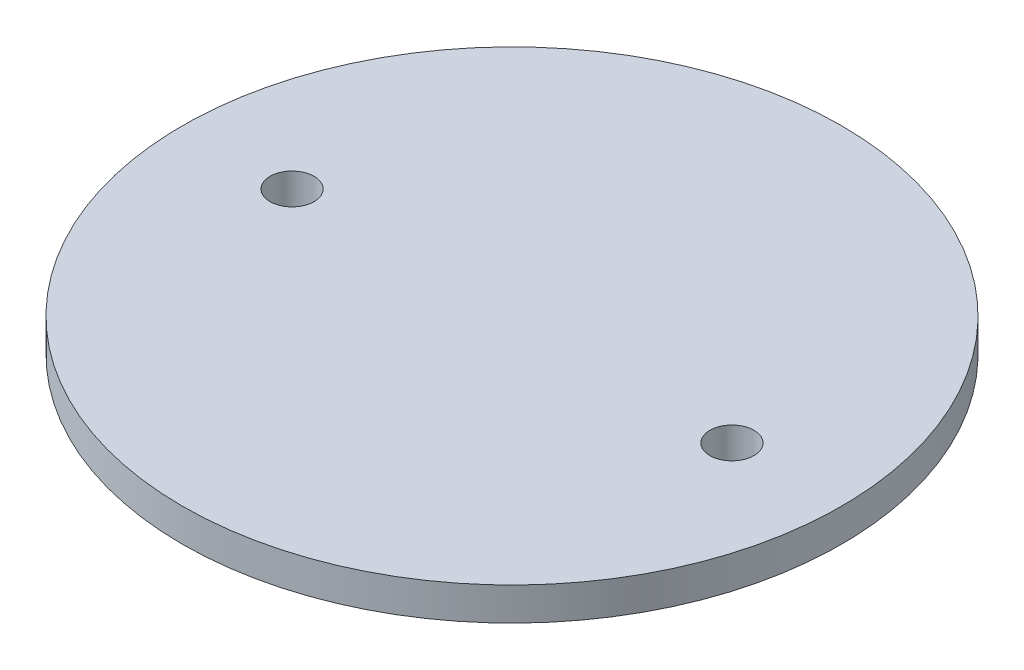
SolidWorks part; units mm, degrees
ref_plane "Front Plane" through (0, 0, 0) normal (0, 0, 1) x (1, 0, 0)
ref_plane "Top Plane" through (0, 0, 0) normal (0, 1, 0) x (1, 0, 0)
ref_plane "Right Plane" through (0, 0, 0) normal (1, 0, 0) x (0, 0, -1)
sketch "Sketch1" plane through (0, 0, 0) normal (0, 1, 0) x (1, 0, 0)
  circle A0 centre (0, 0) radius 47.575
  dimension "D1" = 95.15
extrude "Boss-Extrude1" add sketch "Sketch1" along normal blind 4.7625
sketch "Sketch2" plane through (0, 4.7625, 0) normal (0, 1, 0) x (1, 0, 0)
  circle A0 centre (31.75, 0) radius 3.175
  circle A1 centre (-31.75, 0) radius 3.175
  dimension "D1" = 6.35
  dimension "D2" = 6.35
  dimension "D3" = 31.75
  dimension "D4" = 31.75
extrude "Cut-Extrude1" cut sketch "Sketch2" against normal through all
